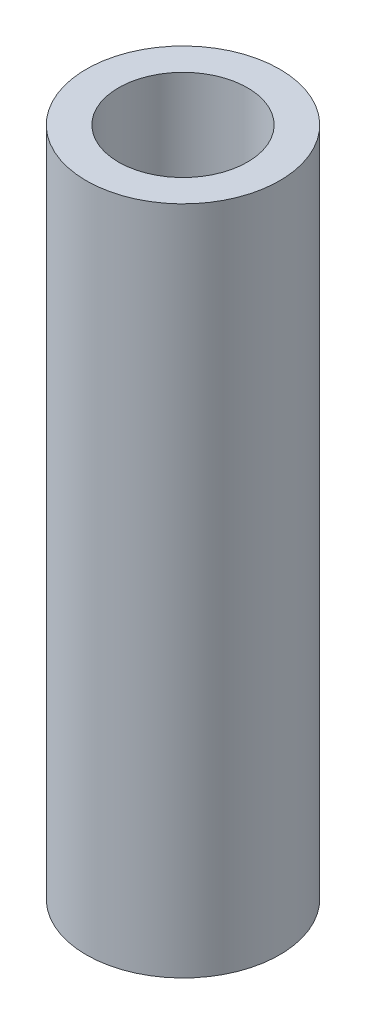
SolidWorks part; units mm, degrees
material "6061-T6 (SS)"
ref_plane "X-Y Datum" through (0, 0, 0) normal (0, 0, 1) x (1, 0, 0)
ref_plane "X-Z Datum" through (0, 0, 0) normal (0, 1, 0) x (1, 0, 0)
ref_plane "Y-Z Datum" through (0, 0, 0) normal (1, 0, 0) x (0, 0, -1)
sketch "Sketch1" plane through (0, 0, 0) normal (0, 1, 0) x (1, 0, 0)
  circle A0 centre (0, 0) radius 3.175
  circle A1 centre (0, 0) radius 4.7625
  dimension "D1" = 6.35
  dimension "D2" = 9.525
  dimension "D3" = 1.5875
extrude "Boss-Extrude1" add sketch "Sketch1" against normal blind 33.02
